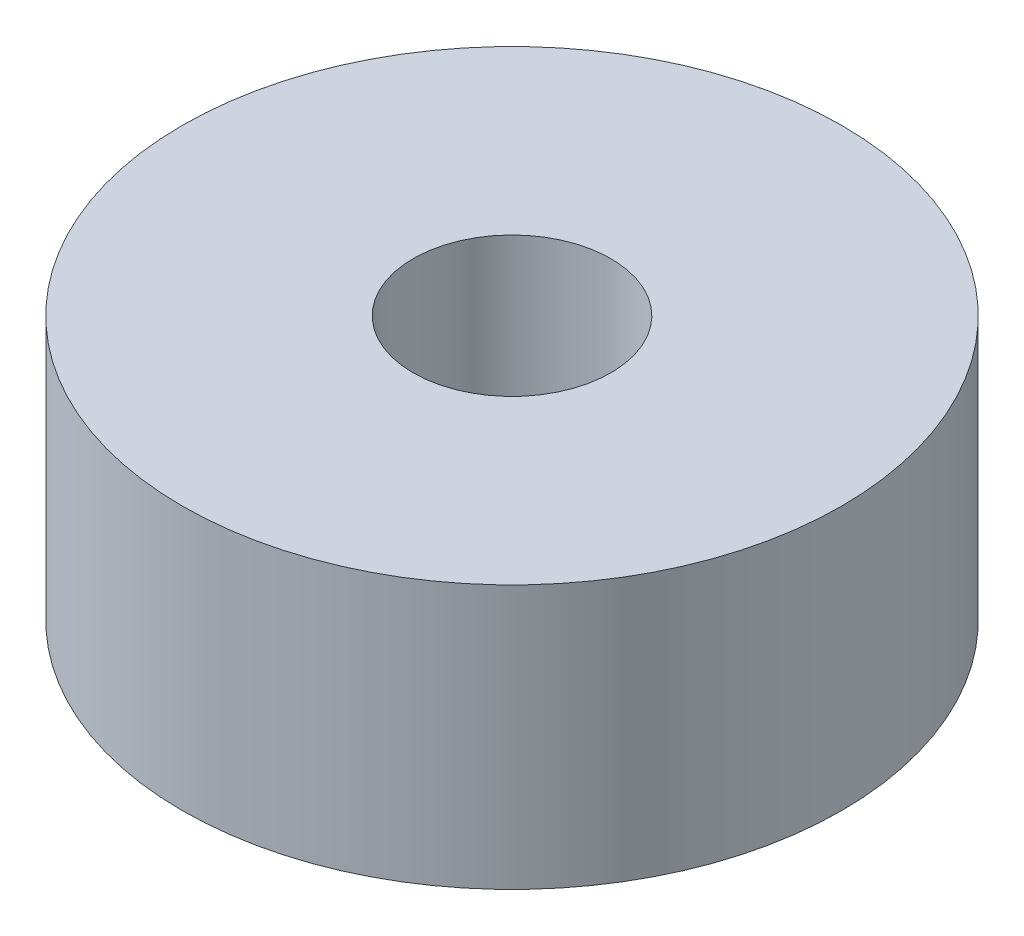
SolidWorks part; units mm, degrees
material "不锈钢 (铁素体)"
ref_plane "前视基准面" through (0, 0, 0) normal (0, 0, 1) x (1, 0, 0)
ref_plane "上视基准面" through (0, 0, 0) normal (0, 1, 0) x (1, 0, 0)
ref_plane "右视基准面" through (0, 0, 0) normal (1, 0, 0) x (0, 0, -1)
sketch "草图1" plane through (0, 0, 0) normal (0, 1, 0) x (1, 0, 0)
  circle A0 centre (0, 0) radius 1.5
  circle A1 centre (0, 0) radius 5
  dimension "D1" = 10
  dimension "D2" = 3
extrude "凸台-拉伸1" add sketch "草图1" along normal blind 4
